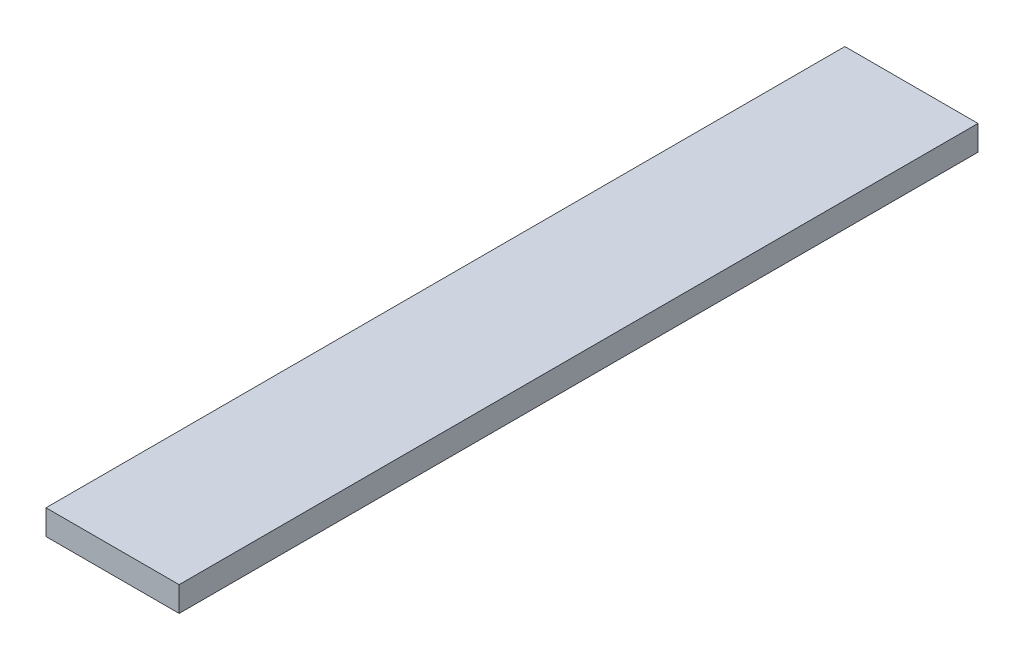
SolidWorks part; units mm, degrees
material "Pine"
ref_plane "Front Plane" through (0, 0, 0) normal (0, 0, 1) x (1, 0, 0)
ref_plane "Top Plane" through (0, 0, 0) normal (0, 1, 0) x (1, 0, 0)
ref_plane "Right Plane" through (0, 0, 0) normal (1, 0, 0) x (0, 0, -1)
sketch "Sketch1" plane through (0, 0, 0) normal (0, 1, 0) x (1, 0, 0)
  line L1 (-50.8, 304.8) -> (50.8, 304.8)
  line L2 (-50.8, 304.8) -> (-50.8, -304.8)
  line L3 (-50.8, -304.8) -> (50.8, -304.8)
  line L4 (50.8, 304.8) -> (50.8, -304.8)
  line L5 (-50.8, 304.8) -> (50.8, -304.8) construction
  line L6 (-50.8, -304.8) -> (50.8, 304.8) construction
  point P0 (0, 0)
  dimension "D1" = 609.6
  dimension "D2" = 101.6
extrude "Boss-Extrude1" add sketch "Sketch1" along normal blind 19.05
